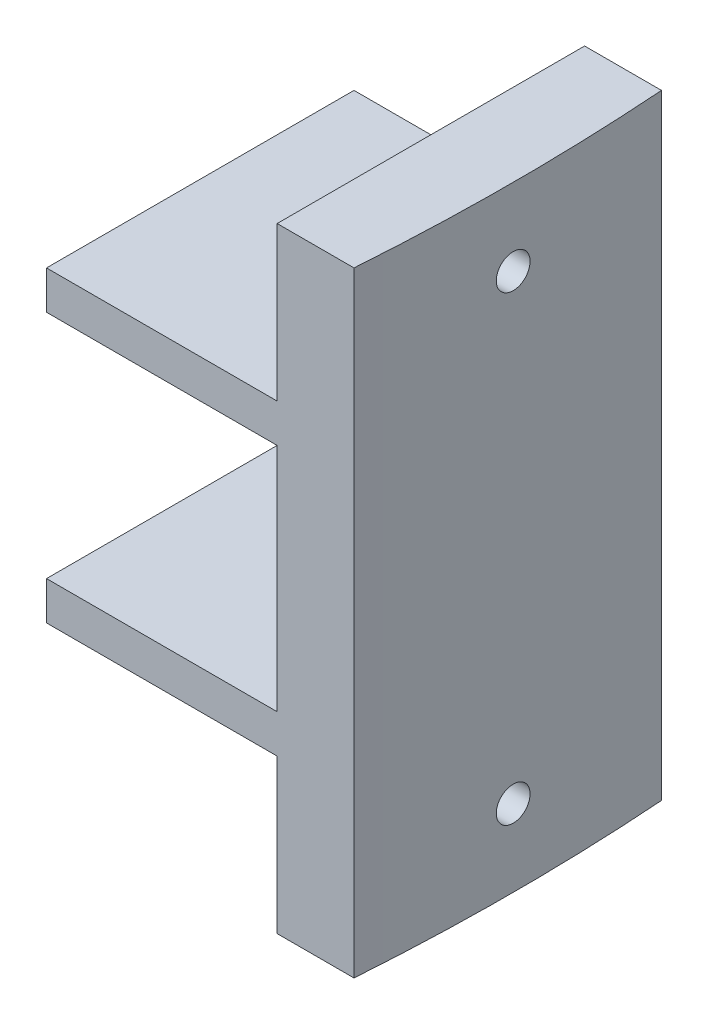
SolidWorks part; units mm, degrees
ref_plane "Front Plane" through (0, 0, 0) normal (0, 0, 1) x (1, 0, 0)
ref_plane "Top Plane" through (0, 0, 0) normal (0, 1, 0) x (1, 0, 0)
ref_plane "Right Plane" through (0, 0, 0) normal (1, 0, 0) x (0, 0, -1)
sketch "Sketch1" plane through (0, 0, 0) normal (0, 1, 0) x (1, 0, 0)
  line L0 (75.9729, 0) -> (82.3229, 0) construction
  line L1 (75.9729, -6.35) -> (88.6729, -6.35)
  line L3 (75.9729, 6.35) -> (88.6729, 6.35)
  line L7 (88.6729, 6.35) -> (75.9729, 6.35)
  line L8 (88.6729, 6.35) -> (88.6729, 4.6501)
  line L9 (88.6729, -6.35) -> (75.9729, -6.35)
  line L10 (75.9729, 6.35) -> (75.9729, -6.35)
  line L11 (75.9729, 3.7178) -> (88.7779, 4.6578) construction
  line L12 (75.9729, -3.7178) -> (88.778, -4.6552) construction
  arc A0 (88.6729, -6.35) -> (88.6729, 6.35) centre (0, 0) ccw
  circle A1 centre (82.3229, 0) radius 1.1303
  dimension "D1" = 177.8
  dimension "D5" = 2.2606
  dimension "D6" = 82.3229
  dimension "D2" = 12.7
  dimension "D3" = 12.7
  dimension "D4" = 6.35
extrude "Boss-Extrude1" add sketch "Sketch1" along normal blind 12.7 contours L3 L10 L1 L8 A1
sketch "Sketch2" plane through (0, 0, 6.35) normal (0, 0, 1) x (1, 0, 0)
  line L1 (75.9729, 1.5875) -> (85.4979, 1.5875)
  line L3 (75.9729, 11.1125) -> (85.4979, 11.1125)
  line L4 (75.9729, 0) -> (88.6729, 0)
  line L5 (88.6729, 0) -> (88.6729, 12.7)
  line L6 (88.6729, 12.7) -> (75.9729, 12.7)
  line L7 (75.9729, 12.7) -> (75.9729, 0)
  line L11 (75.9729, 11.1125) -> (75.9729, 1.5875)
  line L12 (85.4979, 1.5875) -> (85.4979, 11.1125)
  line L13 (75.9729, 6.35) -> (85.4979, 11.1125) construction
  line L14 (75.9729, 6.35) -> (85.4979, 1.5875) construction
  point P2 (75.9729, 6.35)
  dimension "D2" = 9.525
  dimension "D3" = 9.525
  dimension "D1" = 0
extrude "Cut-Extrude1" cut sketch "Sketch2" against normal through all
sketch "Sketch3" plane through (0, 12.7, 0) normal (0, 1, 0) x (1, 0, 0)
  line L0 (75.9729, -6.35) -> (88.6729, -6.35) construction
  line L1 (88.6729, 6.35) -> (75.9729, 6.35) construction
  line L7 (85.4979, -6.35) -> (88.6729, -6.35)
  line L8 (88.6729, 6.35) -> (85.4979, 6.35)
  line L13 (85.4979, 6.35) -> (85.4979, -6.35)
  arc A0 (88.6729, -6.35) -> (88.6729, 6.35) centre (0, 0) ccw construction
  arc A1 (88.6729, -6.35) -> (88.6729, 6.35) centre (0, 0) ccw
  dimension "D1" = 3.175
extrude "Boss-Extrude2" add sketch "Sketch3" along normal blind 6.35 and the other way blind 19.05
sketch "Sketch5" plane through (85.4979, 0, 0) normal (-1, 0, 0) x (0, 0, 1)
  line L0 (6.35, 0) -> (-6.35, 0) construction
  line L1 (-6.35, 0) -> (-6.35, -6.35) construction
  line L2 (-6.35, -6.35) -> (6.35, -6.35) construction
  line L3 (6.35, -6.35) -> (6.35, 0) construction
  line L4 (-6.35, 19.05) -> (-6.35, 12.7) construction
  line L5 (-6.35, 12.7) -> (6.35, 12.7) construction
  line L6 (6.35, 12.7) -> (6.35, 19.05) construction
  line L7 (6.35, 19.05) -> (-6.35, 19.05) construction
  line L8 (6.35, 0) -> (-6.35, 0) construction
  line L9 (-6.35, 0) -> (-6.35, -6.35) construction
  line L10 (-6.35, -6.35) -> (6.35, -6.35) construction
  line L11 (6.35, -6.35) -> (6.35, 0) construction
  line L12 (-6.35, 19.05) -> (-6.35, 12.7) construction
  line L13 (-6.35, 12.7) -> (6.35, 12.7) construction
  line L14 (6.35, 12.7) -> (6.35, 19.05) construction
  line L15 (6.35, 19.05) -> (-6.35, 19.05) construction
  line L16 (0, 19.05) -> (0, 12.7) construction
  line L17 (0, 0) -> (0, -6.35) construction
  circle A0 centre (0, 15.875) radius 0.6985
  circle A1 centre (0, -3.175) radius 0.6985
  dimension "D1" = 1.397
extrude "Cut-Extrude2" cut sketch "Sketch5" against normal through all
